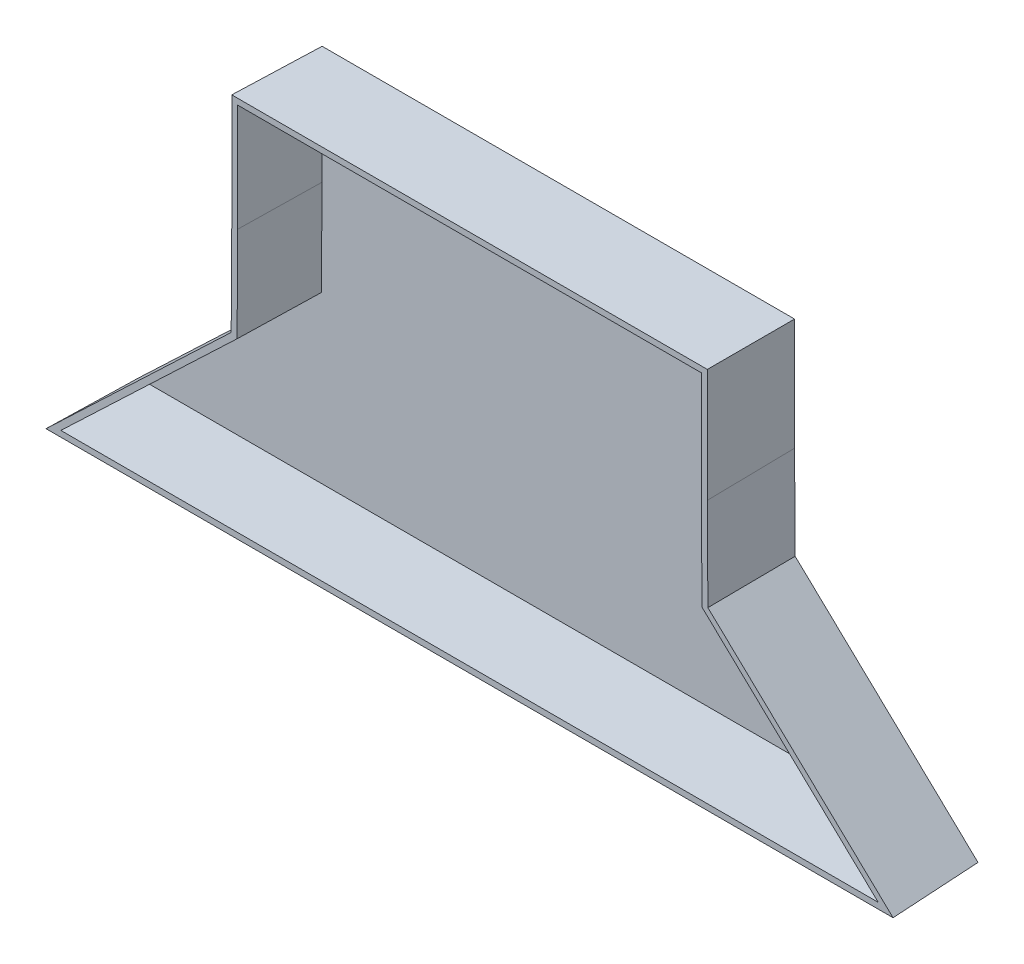
SolidWorks part; units mm, degrees
ref_plane "Front Plane" through (0, 0, 0) normal (0, 0, 1) x (1, 0, 0)
ref_plane "Top Plane" through (0, 0, 0) normal (0, 1, 0) x (1, 0, 0)
ref_plane "Right Plane" through (0, 0, 0) normal (1, 0, 0) x (0, 0, -1)
sketch "Sketch4" plane through (0, 0, 0) normal (0, 0, 1) x (1, 0, 0)
  line L0 (94.6675, 69.5414) -> (94.6675, 4.4133) construction
  line L1 (54.6675, 34.8869) -> (32.7496, 14.0618)
  line L2 (134.6675, 34.8869) -> (156.5854, 14.0618)
  line L3 (45.2911, 5.5414) -> (144.0439, 5.5414)
  line L4 (32.7496, 14.0618) -> (23.7822, 5.5414)
  line L5 (23.7822, 5.5414) -> (45.2911, 5.5414)
  line L6 (156.5854, 14.0618) -> (165.5529, 5.5414)
  line L7 (165.5529, 5.5414) -> (144.0439, 5.5414)
  line L8 (54.6675, 34.8869) -> (54.7664, 50.6478)
  line L9 (54.7664, 50.6478) -> (54.7664, 69.5414)
  line L10 (54.7664, 69.5414) -> (134.5687, 69.5414)
  line L11 (134.6675, 34.8869) -> (134.5687, 50.6478)
  line L12 (134.5687, 50.6478) -> (134.5687, 69.5414)
  point P7 (94.6675, 5.5414)
  point P9 (54.7664, 50.6478)
  point P10 (127.7664, 50.6478)
  dimension "D3" = 0.719
  dimension "D1" = 64
  dimension "D2" = 80
  dimension "D4" = 79.8022
extrude "Boss-Extrude1" add sketch "Sketch4" along normal blind 15 draft 1 draft outward yes
shell "Shell1" thickness 1
